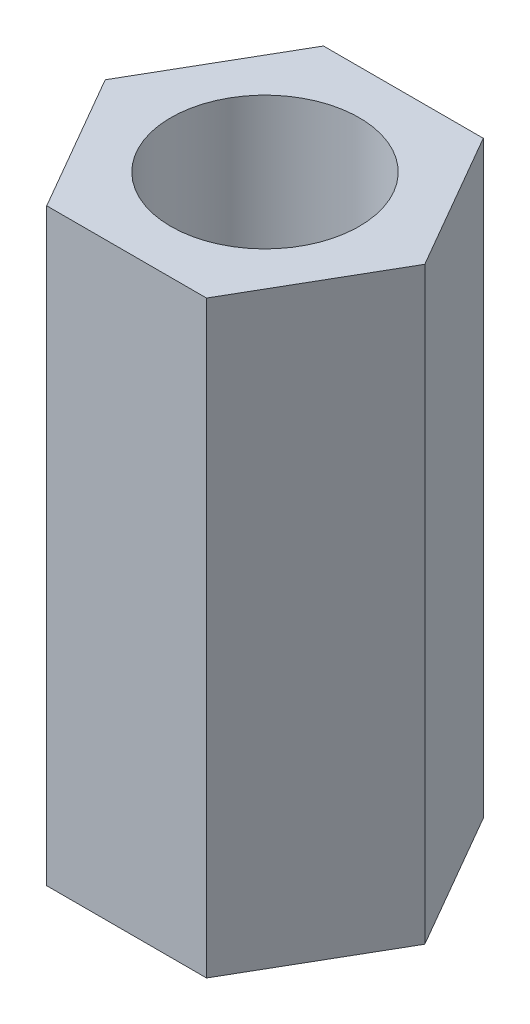
SolidWorks part; units mm, degrees
material "黄铜"
ref_plane "前视基准面" through (0, 0, 0) normal (0, 0, 1) x (1, 0, 0)
ref_plane "上视基准面" through (0, 0, 0) normal (0, 1, 0) x (1, 0, 0)
ref_plane "右视基准面" through (0, 0, 0) normal (1, 0, 0) x (0, 0, -1)
sketch "草图1" plane through (0, 0, 0) normal (0, 1, 0) x (1, 0, 0)
  line L1 (2.7135, 0) -> (1.3568, 2.35)
  line L2 (1.3568, 2.35) -> (-1.3568, 2.35)
  line L3 (-1.3568, 2.35) -> (-2.7135, 0)
  line L4 (-2.7135, 0) -> (-1.3568, -2.35)
  line L5 (-1.3568, -2.35) -> (1.3568, -2.35)
  line L6 (1.3568, -2.35) -> (2.7135, 0)
  circle A0 centre (0, 0) radius 2.35 construction
  dimension "D1" = 4.7
extrude "凸台-拉伸1" add sketch "草图1" along normal blind 10
sketch "草图2" plane through (0, 10, 0) normal (0, 1, 0) x (1, 0, 0)
  circle A0 centre (0, 0) radius 1.6
  dimension "D1" = 3.2
extrude "切除-拉伸1" cut sketch "草图2" against normal through all
